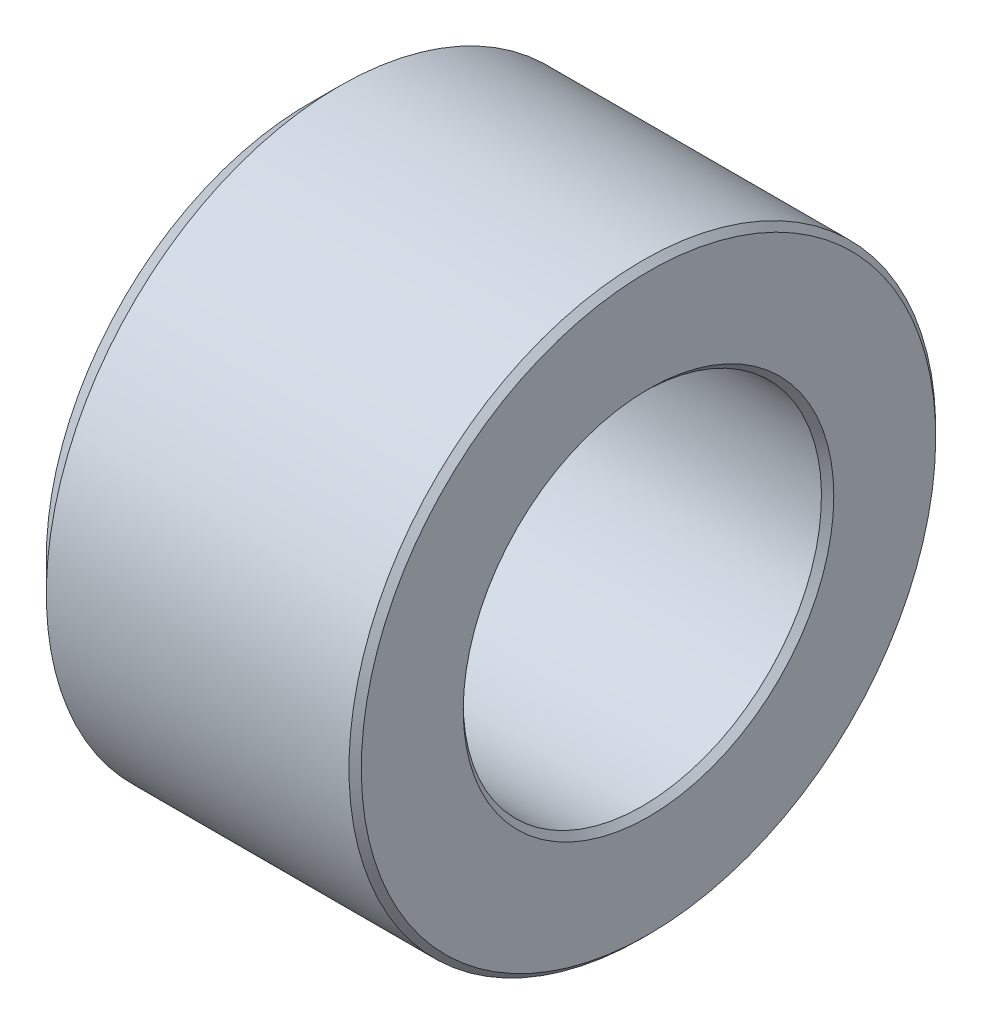
SolidWorks part; units mm, degrees
material "POM copolymère d'acétal"
ref_plane "Plan de face" through (0, 0, 0) normal (0, 0, 1) x (1, 0, 0)
ref_plane "Plan de dessus" through (0, 0, 0) normal (0, 1, 0) x (1, 0, 0)
ref_plane "Plan de droite" through (0, 0, 0) normal (1, 0, 0) x (0, 0, -1)
sketch "Esquisse1" plane through (0, 0, 0) normal (0, 0, 1) x (1, 0, 0)
  line L0 (0, 0) -> (-3, 0)
  line L1 (-2.75, 4.75) -> (2.75, 4.75)
  line L2 (-2.75, 4.75) -> (-2.75, 2.9)
  line L3 (-2.75, 2.9) -> (2.75, 2.9)
  line L4 (2.75, 4.75) -> (2.75, 2.9)
  dimension "D1" = 5.5
  dimension "D2" = 2.9
  dimension "D3" = 4.75
  dimension "D4" = 2.75
  dimension "D5" = 3
revolve "Révolution1" add sketch "Esquisse1" angle 360 about L0
chamfer "Chanfrein1" distance 0.1 angle 45 3 edges at (-2.75, 2.9, 0) (2.75, 4.75, 0) (2.75, 2.9, 0)
chamfer "Chanfrein2" distance 0.5 angle 45 1 edges at (-2.75, 4.75, 0)
equation "\"D4@Esquisse1\" = \"D1@Esquisse1\"/2"
